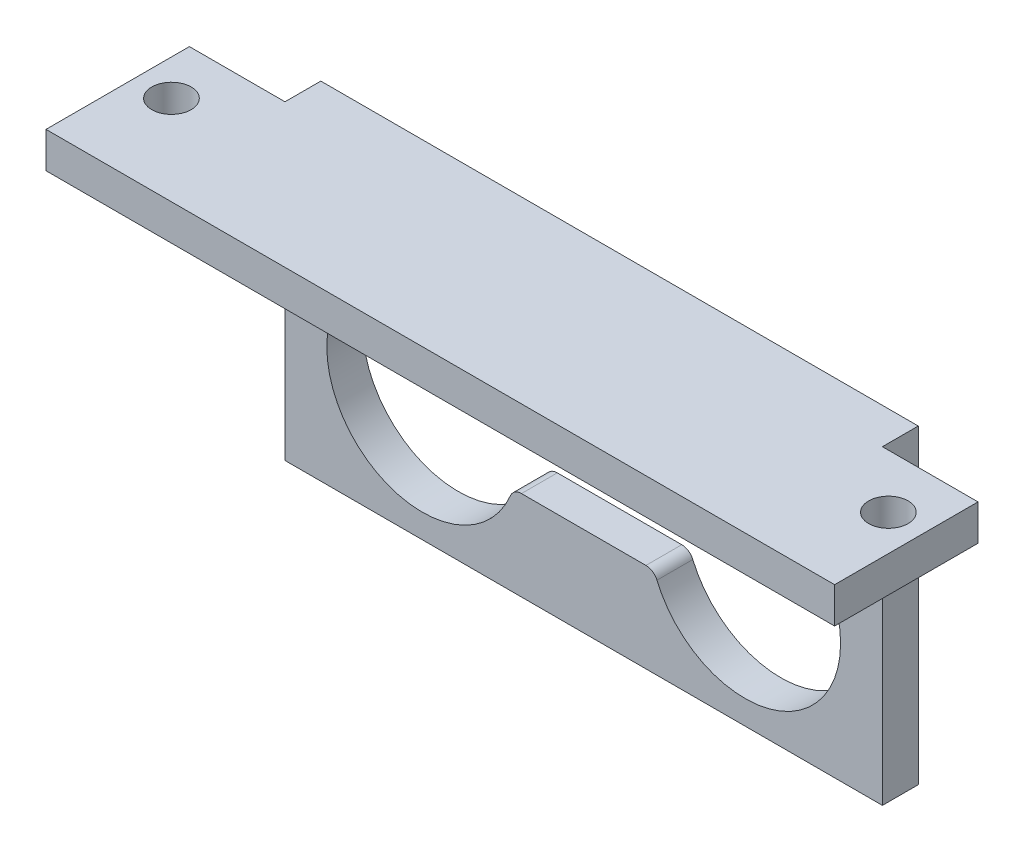
SolidWorks part; units mm, degrees
ref_plane "前视基准面" through (0, 0, 0) normal (0, 0, 1) x (1, 0, 0)
ref_plane "上视基准面" through (0, 0, 0) normal (0, 1, 0) x (1, 0, 0)
ref_plane "右视基准面" through (0, 0, 0) normal (1, 0, 0) x (0, 0, -1)
sketch "草图1" plane through (0, 0, 0) normal (0, 0, 1) x (1, 0, 0)
  line L1 (25, -10) -> (-25, -10)
  line L2 (25, -10) -> (25, 10)
  line L3 (25, 10) -> (-25, 10)
  line L4 (-25, -10) -> (-25, 10)
  line L5 (25, -10) -> (-25, 10) construction
  line L6 (25, 10) -> (-25, -10) construction
  line L8 (-5.2084, 2.5) -> (5.2084, 2.5)
  line L9 (5.2084, -2.5) -> (-5.2084, -2.5)
  line L10 (3.25, 7.25) -> (-3.25, 7.25) construction
  line L11 (3.25, 5.5) -> (-3.25, 5.5)
  line L12 (3.25, 9) -> (-3.25, 9)
  arc A7 (6.1297, -3.1111) -> (6.1297, 3.1111) centre (13.5, 0) ccw
  arc A8 (-6.1297, 3.1111) -> (-6.1297, -3.1111) centre (-13.5, 0) ccw
  arc A9 (5.2084, -2.5) -> (6.1297, -3.1111) centre (5.2084, -3.5) cw
  arc A10 (5.2084, 2.5) -> (6.1297, 3.1111) centre (5.2084, 3.5) ccw
  arc A11 (-5.2084, -2.5) -> (-6.1297, -3.1111) centre (-5.2084, -3.5) ccw
  arc A12 (-5.2084, 2.5) -> (-6.1297, 3.1111) centre (-5.2084, 3.5) cw
  arc A13 (3.25, 5.5) -> (3.25, 9) centre (3.25, 7.25) ccw
  arc A14 (-3.25, 9) -> (-3.25, 5.5) centre (-3.25, 7.25) ccw
  point P0 (0, 0)
  point P22 (0, 7.25)
  dimension "D3" = 1
  dimension "D4" = 8
  dimension "D5" = 8
  dimension "D6" = 2.5
  dimension "D8" = 13.5
  dimension "D9" = 13.5
  dimension "D12" = 1.75
  dimension "D1" = 20
  dimension "D2" = 50
  dimension "D7" = 2.5
  dimension "D10" = 7.25
  dimension "D11" = 6.5
  dimension "D13" = 3.25
extrude "凸台-拉伸1" add sketch "草图1" along normal blind 3
sketch "草图2" plane through (0, 10, 0) normal (0, 1, 0) x (1, 0, 0)
  line L1 (-25, 0) -> (25, 0)
  line L2 (-25, 0) -> (-25, -15)
  line L3 (-25, -15) -> (25, -15)
  line L4 (25, 0) -> (25, -15)
  dimension "D1" = 15
extrude "凸台-拉伸2" add sketch "草图2" along normal blind 6
sketch "草图5" plane through (0, 10, 0) normal (0, -1, 0) x (1, 0, 0)
  line L1 (25, 3) -> (-25, 3)
  line L2 (25, 3) -> (25, 15)
  line L3 (25, 15) -> (-25, 15)
  line L4 (-25, 3) -> (-25, 15)
extrude "切除-拉伸2" cut sketch "草图5" against normal blind 3
sketch "草图6" plane through (0, 16, 0) normal (0, 1, 0) x (1, 0, 0)
  line L1 (25, -15) -> (33, -15)
  line L2 (25, -15) -> (25, -3)
  line L3 (25, -3) -> (33, -3)
  line L4 (33, -15) -> (33, -3)
  line L5 (-25, -15) -> (-33, -15)
  line L6 (-25, -15) -> (-25, -3)
  line L7 (-25, -3) -> (-33, -3)
  line L8 (-33, -15) -> (-33, -3)
  circle A0 centre (30, -7.5) radius 1.65
  circle A1 centre (-30, -7.5) radius 1.65
  dimension "D5" = 3.3
  dimension "D6" = 3.3
  dimension "D1" = 12
  dimension "D2" = 8
  dimension "D3" = 8
  dimension "D4" = 12
extrude "凸台-拉伸3" add sketch "草图6" against normal blind 3
